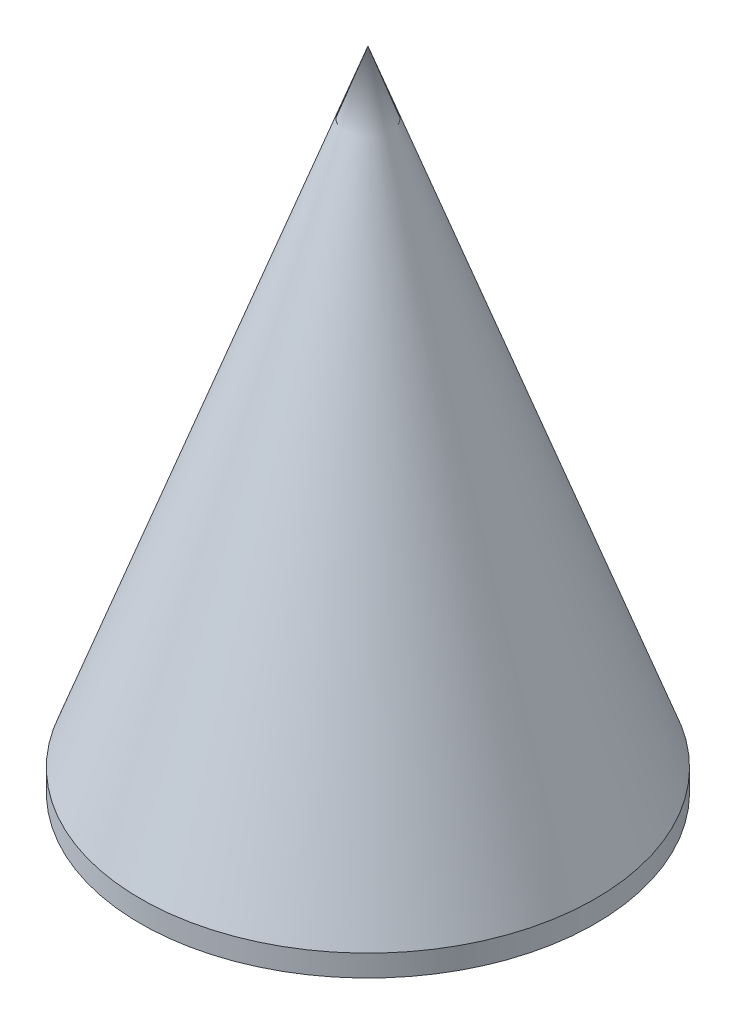
SolidWorks part; units mm, degrees
ref_plane "Front Plane" through (0, 0, 0) normal (0, 0, 1) x (1, 0, 0)
ref_plane "Top Plane" through (0, 0, 0) normal (0, 1, 0) x (1, 0, 0)
ref_plane "Right Plane" through (0, 0, 0) normal (1, 0, 0) x (0, 0, -1)
sketch "Sketch1" plane through (0, 0, 0) normal (0, 0, 1) x (1, 0, 0)
  line L0 (0, 0) -> (0, 65.3751) construction
  line L1 (-1.5875, 0) -> (-22.225, 0)
  line L2 (-22.225, 0) -> (-22.225, 2.1082)
  line L3 (-1.5875, 2.1082) -> (-1.5875, 6.35)
  line L4 (-1.5875, 0) -> (-1.5875, 2.1082)
  line L5 (-6.35, 2.1082) -> (-21.1836, 2.1082)
  line L6 (-22.225, 2.1082) -> (0, 63.1709)
  line L7 (0, 63.1709) -> (0, 60.3097)
  line L8 (0, 60.3097) -> (-21.1836, 2.1082)
  line L10 (-1.5875, 6.35) -> (-6.35, 6.35)
  line L11 (-6.35, 6.35) -> (-6.35, 2.1082)
  dimension "D1" = 1.0414
  dimension "D2" = 3.175
  dimension "D3" = 70
  dimension "D4" = 2.1082
  dimension "D5" = 6.35
  dimension "D6" = 44.45
  dimension "D7" = 12.7
revolve "Revolve1" add sketch "Sketch1" angle 360 about L0
